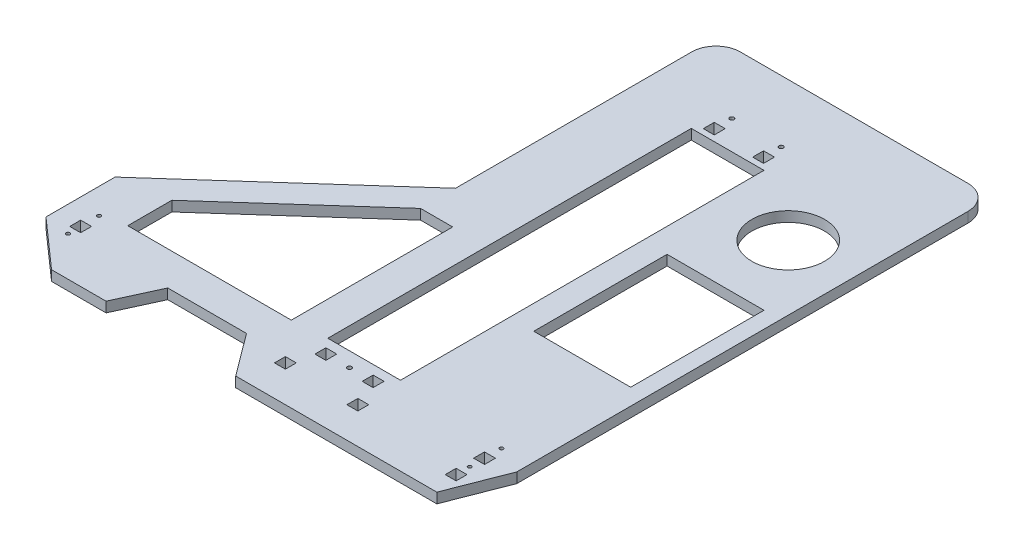
SolidWorks part; units mm, degrees
ref_plane "Front Plane" through (0, 0, 0) normal (0, 0, 1) x (1, 0, 0)
ref_plane "Top Plane" through (0, 0, 0) normal (0, 1, 0) x (1, 0, 0)
ref_plane "Right Plane" through (0, 0, 0) normal (1, 0, 0) x (0, 0, -1)
sketch "Sketch1" plane through (0, 0, 0) normal (0, 1, 0) x (1, 0, 0)
  line L0 (0, 0) -> (-228, 0)
  line L1 (-228, 0) -> (-228, -215)
  line L2 (-228, -215) -> (-376.5, -347.4717)
  line L3 (-376.5, -347.4717) -> (-376.5, -404.4717)
  line L4 (-376.5, -404.4717) -> (-336.5, -439.9)
  line L5 (-336.5, -439.9) -> (-291.5, -439.9)
  line L6 (-291.5, -439.9) -> (-275.5, -405)
  line L7 (-275.5, -405) -> (-210.5, -405)
  line L8 (-210.5, -405) -> (-184.5, -439.9)
  line L9 (-184.5, -439.9) -> (-18.5, -439.9)
  line L10 (-18.5, -439.9) -> (0, -392.4)
  line L11 (0, -392.4) -> (0, 0)
  line L12 (-291.5, -439.9) -> (-184.5, -439.9) construction
  dimension "D1" = 45
  dimension "D2" = 65
  dimension "D3" = 228
  dimension "D4" = 215
  dimension "D5" = 57
  dimension "D6" = 18.5
  dimension "D7" = 34.9
  dimension "D8" = 166
  dimension "D9" = 47.5
  dimension "D10" = 16
  dimension "D11" = 26
  dimension "D12" = 40
  dimension "D13" = 190
  dimension "D14" = 199
extrude "Boss-Extrude1" add sketch "Sketch1" along normal blind 8.4
sketch "Sketch2" plane through (0, 8.4, 0) normal (0, 1, 0) x (1, 0, 0)
  line L0 (-228, -215) -> (-228, -405) construction
  line L1 (-275.5, -405) -> (-210.5, -405) construction
  line L2 (-336.5, -439.9) -> (-336.5, -311.7891) construction
  line L3 (-228, -215) -> (-376.5, -347.4717) construction
  line L4 (-336.5, -340.6005) -> (-228, -243.8114)
  line L5 (-228, -243.8114) -> (-201.5, -243.8114)
  line L6 (-201.5, -243.8114) -> (-201.5, -377)
  line L7 (-201.5, -377) -> (-336.5, -377)
  line L8 (-336.5, -377) -> (-336.5, -340.6005)
  line L9 (-184.5, -439.9) -> (-18.5, -439.9) construction
  line L10 (-173.5, -374.9) -> (-113.5, -374.9)
  line L11 (-173.5, -374.9) -> (-173.5, -74.9)
  line L12 (-173.5, -74.9) -> (-113.5, -74.9)
  line L13 (-113.5, -374.9) -> (-113.5, -74.9)
  line L15 (-23.1, -439.9) -> (-23.1, 0) construction
  line L16 (0, 0) -> (-228, 0) construction
  line L17 (-355.4, -423.1601) -> (-355.4, -328.6491) construction
  line L18 (-27.6, -423.9) -> (-18.6, -423.9)
  line L19 (-27.6, -423.9) -> (-27.6, -414.9)
  line L20 (-27.6, -414.9) -> (-18.6, -414.9)
  line L21 (-18.6, -423.9) -> (-18.6, -414.9)
  line L22 (-27.6, -423.9) -> (-18.6, -414.9) construction
  line L23 (-27.6, -414.9) -> (-18.6, -423.9) construction
  line L24 (-27.6, -400.45) -> (-18.6, -400.45)
  line L25 (-27.6, -400.45) -> (-27.6, -391.45)
  line L26 (-27.6, -391.45) -> (-18.6, -391.45)
  line L27 (-18.6, -400.45) -> (-18.6, -391.45)
  line L28 (-27.6, -400.45) -> (-18.6, -391.45) construction
  line L29 (-27.6, -391.45) -> (-18.6, -400.45) construction
  line L30 (-376.5, -404.4717) -> (-336.5, -439.9) construction
  line L31 (-376.5, -347.4717) -> (-376.5, -404.4717) construction
  line L32 (-350.9, -392.4717) -> (-359.9, -392.4717)
  line L33 (-350.9, -392.4717) -> (-350.9, -401.4717)
  line L34 (-350.9, -401.4717) -> (-359.9, -401.4717)
  line L35 (-359.9, -392.4717) -> (-359.9, -401.4717)
  line L36 (-350.9, -392.4717) -> (-359.9, -401.4717) construction
  line L37 (-350.9, -401.4717) -> (-359.9, -392.4717) construction
  line L39 (0, -392.4) -> (0, 0) construction
  line L40 (-173.024, -65.6) -> (-113.024, -65.6) construction
  line L41 (-143.5, -74.9) -> (-143.5, -65.6) construction
  line L42 (-168.35, -61.1) -> (-159.35, -61.1)
  line L43 (-168.35, -61.1) -> (-168.35, -70.1)
  line L44 (-168.35, -70.1) -> (-159.35, -70.1)
  line L45 (-159.35, -61.1) -> (-159.35, -70.1)
  line L46 (-168.35, -61.1) -> (-159.35, -70.1) construction
  line L47 (-168.35, -70.1) -> (-159.35, -61.1) construction
  line L48 (-118.65, -70.1) -> (-127.65, -61.1) construction
  line L49 (-118.65, -61.1) -> (-127.65, -70.1) construction
  line L50 (-127.65, -61.1) -> (-127.65, -70.1)
  line L51 (-118.65, -70.1) -> (-127.65, -70.1)
  line L52 (-118.65, -61.1) -> (-118.65, -70.1)
  line L53 (-118.65, -61.1) -> (-127.65, -61.1)
  line L54 (-163.85, -65.6) -> (-163.85, -51.1) construction
  line L55 (-123.15, -65.6) -> (-123.15, -51.1) construction
  line L56 (-143.5, -374.9) -> (-143.5, -439.9) construction
  line L57 (-163, -387) -> (-124, -387) construction
  line L58 (-119.5, -391.5) -> (-128.5, -382.5) construction
  line L59 (-167.5, -382.5) -> (-158.5, -382.5)
  line L60 (-167.5, -382.5) -> (-167.5, -391.5)
  line L61 (-167.5, -391.5) -> (-158.5, -391.5)
  line L62 (-158.5, -382.5) -> (-158.5, -391.5)
  line L63 (-167.5, -382.5) -> (-158.5, -391.5) construction
  line L64 (-167.5, -391.5) -> (-158.5, -382.5) construction
  line L65 (-119.5, -382.5) -> (-128.5, -391.5) construction
  line L66 (-128.5, -382.5) -> (-128.5, -391.5)
  line L67 (-119.5, -391.5) -> (-128.5, -391.5)
  line L68 (-119.5, -382.5) -> (-119.5, -391.5)
  line L69 (-119.5, -382.5) -> (-128.5, -382.5)
  line L70 (-109.1, -414.5) -> (-118.1, -405.5) construction
  line L71 (-177.9, -405.5) -> (-168.9, -405.5)
  line L72 (-177.9, -405.5) -> (-177.9, -414.5)
  line L73 (-177.9, -414.5) -> (-168.9, -414.5)
  line L74 (-168.9, -405.5) -> (-168.9, -414.5)
  line L75 (-177.9, -405.5) -> (-168.9, -414.5) construction
  line L76 (-177.9, -414.5) -> (-168.9, -405.5) construction
  line L77 (-109.1, -405.5) -> (-118.1, -414.5) construction
  line L78 (-118.1, -405.5) -> (-118.1, -414.5)
  line L79 (-109.1, -414.5) -> (-118.1, -414.5)
  line L80 (-109.1, -405.5) -> (-109.1, -414.5)
  line L81 (-109.1, -405.5) -> (-118.1, -405.5)
  circle A0 centre (-23.1, -408.2) radius 1.5
  circle A1 centre (-23.1, -382) radius 1.5
  circle A2 centre (-355.4, -407.3717) radius 1.5
  circle A3 centre (-355.4, -381.7717) radius 1.5
  circle A4 centre (-163.85, -51.1) radius 1.75
  circle A5 centre (-123.15, -51.1) radius 1.75
  circle A6 centre (-143.5, -387) radius 1.75
  point P25 (-23.1, -419.4)
  point P30 (-23.1, -395.95)
  point P44 (-355.4, -396.9717)
  point P61 (-163.85, -65.6)
  point P72 (-123.15, -65.6)
  point P85 (-163, -387)
  point P94 (-124, -387)
  point P95 (-173.4, -410)
  point P104 (-113.6, -410)
  dimension "D13" = 3
  dimension "D14" = 3
  dimension "D23" = 3
  dimension "D24" = 3
  dimension "D31" = 3.5
  dimension "D34" = 3.5
  dimension "D1" = 21.5
  dimension "D2" = 28
  dimension "D3" = 26.5
  dimension "D4" = 60
  dimension "D5" = 300
  dimension "D6" = 65
  dimension "D7" = 28
  dimension "D8" = 9
  dimension "D9" = 9
  dimension "D10" = 9
  dimension "D11" = 9
  dimension "D12" = 23.45
  dimension "D15" = 26.2
  dimension "D16" = 11.2
  dimension "D17" = 16
  dimension "D18" = 18.6
  dimension "D19" = 9
  dimension "D20" = 9
  dimension "D21" = 3
  dimension "D22" = 16.6
  dimension "D25" = 25.6
  dimension "D26" = 10.4
  dimension "D27" = 9
  dimension "D28" = 9
  dimension "D29" = 31.7
  dimension "D30" = 4.8
  dimension "D32" = 10
  dimension "D33" = 9
  dimension "D35" = 39
  dimension "D36" = 7.6
  dimension "D37" = 0
  dimension "D38" = 9
  dimension "D39" = 9
  dimension "D40" = 10.4
  dimension "D41" = 23
extrude "Cut-Extrude1" cut sketch "Sketch2" against normal through all
fillet "Fillet1" radius 20 2 edges at (0, 4.2, 0) (-228, 4.2, 0)
sketch "Sketch3" plane through (0, 8.4, 0) normal (0, 1, 0) x (1, 0, 0)
  line L0 (-53.5, 0) -> (-53.5, -439.9) construction
  line L1 (-20, 0) -> (-208, 0) construction
  line L2 (-184.5, -439.9) -> (-18.5, -439.9) construction
  line L3 (-113.5, -74.9) -> (-173.5, -74.9) construction
  line L4 (-113.5, -374.9) -> (-113.5, -74.9) construction
  line L6 (-93.5, -284.9) -> (-13.5, -284.9)
  line L7 (-93.5, -284.9) -> (-93.5, -174.9)
  line L8 (-93.5, -174.9) -> (-13.5, -174.9)
  line L9 (-13.5, -284.9) -> (-13.5, -174.9)
  line L10 (-93.5, -284.9) -> (-13.5, -174.9) construction
  line L11 (-93.5, -174.9) -> (-13.5, -284.9) construction
  circle A0 centre (-53.5, -114.9) radius 30
  point P8 (-143.5, -74.9)
  point P13 (-53.5, -229.9)
  dimension "D1" = 60
  dimension "D2" = 40
  dimension "D3" = 60
  dimension "D4" = 80
  dimension "D5" = 110
  dimension "D6" = 60
extrude "Cut-Extrude2" cut sketch "Sketch3" against normal through all
